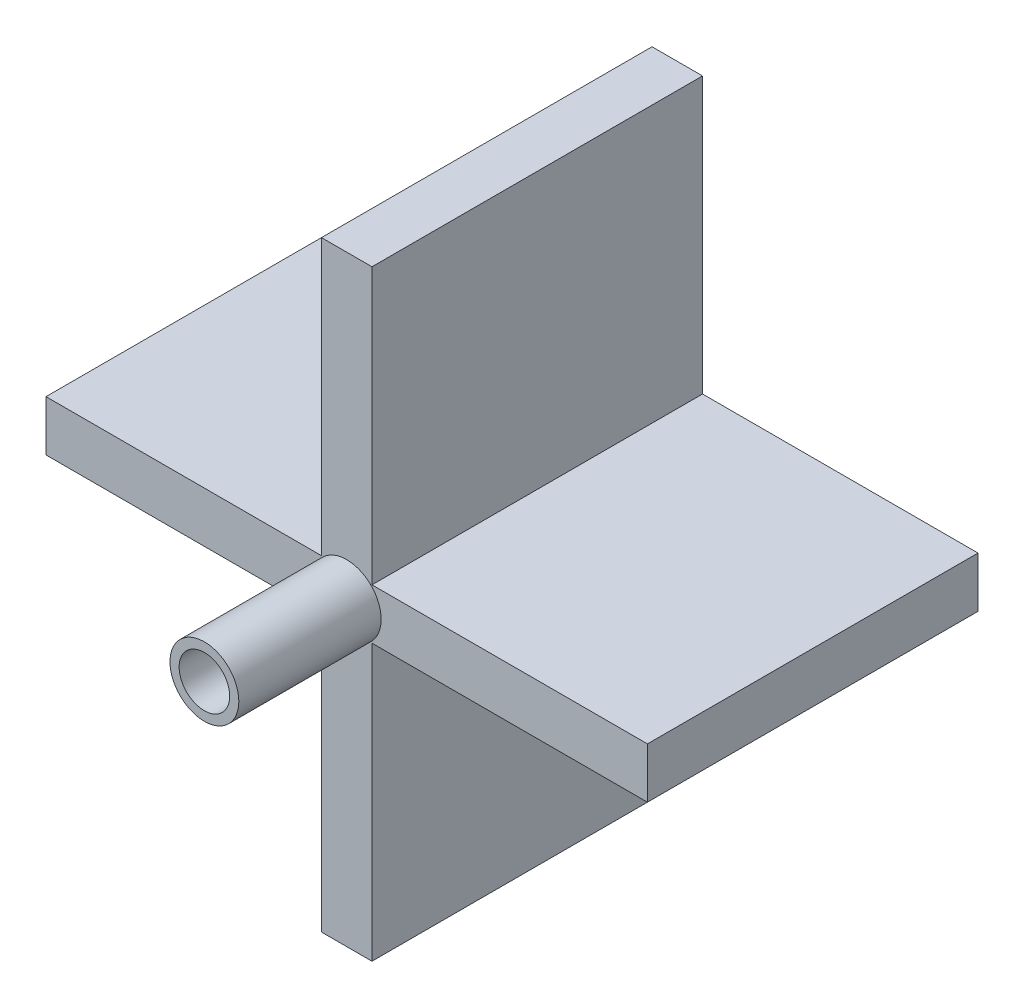
SolidWorks part; units mm, degrees
ref_plane "前基準面" through (0, 0, 0) normal (0, 0, 1) x (1, 0, 0)
ref_plane "上基準面" through (0, 0, 0) normal (0, 1, 0) x (1, 0, 0)
ref_plane "右基準面" through (0, 0, 0) normal (1, 0, 0) x (0, 0, -1)
sketch "草圖1" plane through (0, 0, 0) normal (0, 0, 1) x (1, 0, 0)
  line L1 (-46.6516, 8.241) -> (18.8484, 8.241)
  line L2 (-46.6516, 8.241) -> (-46.6516, 2.741)
  line L3 (-46.6516, 2.741) -> (18.8484, 2.741)
  line L4 (18.8484, 8.241) -> (18.8484, 2.741)
  line L5 (-16.6516, 38.241) -> (-11.1516, 38.241)
  line L6 (-16.6516, 38.241) -> (-16.6516, -27.259)
  line L7 (-16.6516, -27.259) -> (-11.1516, -27.259)
  line L8 (-11.1516, 38.241) -> (-11.1516, -27.259)
  dimension "D1" = 65.5
  dimension "D2" = 30
  dimension "D3" = 5.5
  dimension "D4" = 5.5
  dimension "D5" = 30
  dimension "D6" = 65.5
extrude "填料-伸長1" add sketch "草圖1" along normal blind 36 contours L8 L5 L6 L1 | L6 L1 L2 L3 | L8 L3 L6 L7 | L1 L8 L3 L4 | L8 L1 L6 L3
sketch "草圖5" plane through (0, 0, 36) normal (0, 0, 1) x (1, 0, 0)
  line L0 (-16.6516, 38.241) -> (-16.6516, 8.241) construction
  line L1 (-46.6516, 2.741) -> (-16.6516, 2.741) construction
  circle A0 centre (-13.9016, 5.491) radius 3.75
  dimension "D1" = 7.5
  dimension "D2" = 2.75
  dimension "D3" = 2.75
extrude "填料-伸長3" add sketch "草圖5" along normal blind 15.5
sketch "草圖6" plane through (0, 0, 0) normal (0, 0, -1) x (-1, 0, 0)
  circle A0 centre (13.9016, 5.491) radius 2.85
  dimension "D1" = 5.7
extrude "除料-伸長1" cut sketch "草圖6" against normal blind 5
sketch "草圖7" plane through (0, 0, 51.5) normal (0, 0, 1) x (1, 0, 0)
  circle A0 centre (-13.9016, 5.491) radius 1.75
  dimension "D1" = 3.5
extrude "除料-伸長2" cut sketch "草圖7" against normal through all
sketch "草圖8" plane through (0, 0, 51.5) normal (0, 0, 1) x (1, 0, 0)
  circle A0 centre (-13.9016, 5.491) radius 2.75
  dimension "D1" = 5.5
extrude "除料-伸長3" cut sketch "草圖8" against normal blind 10
